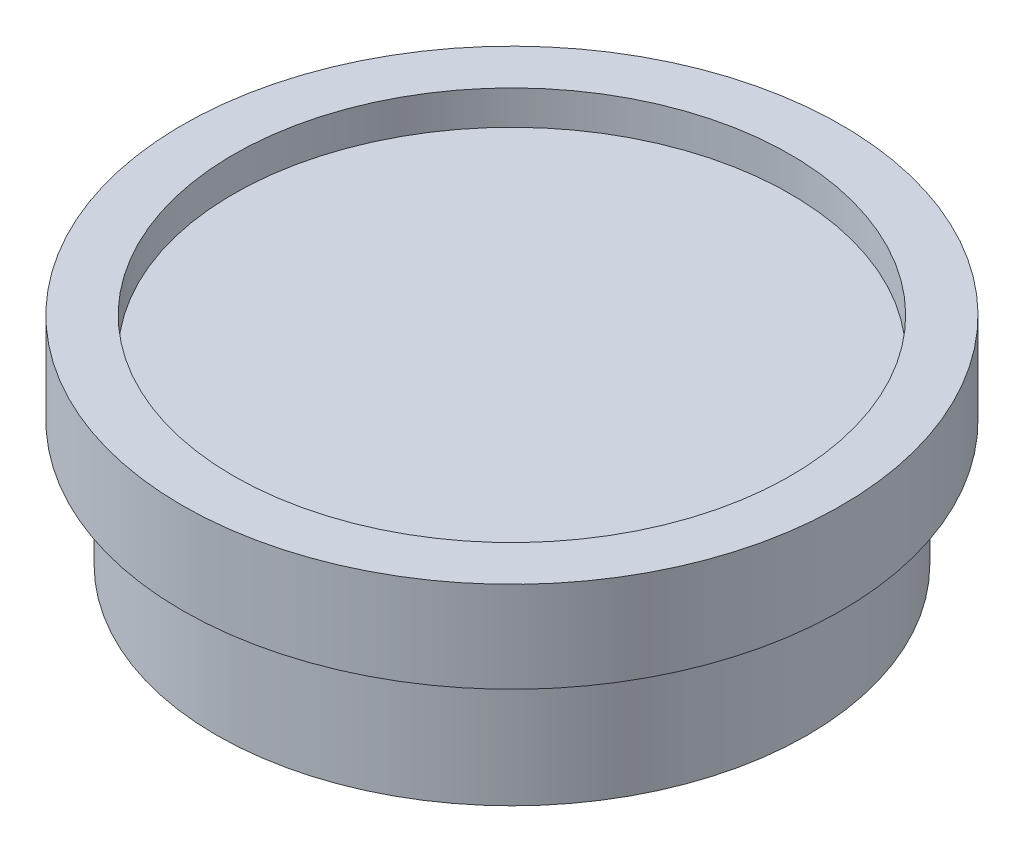
SolidWorks part; units mm, degrees
ref_plane "Front Plane" through (0, 0, 0) normal (0, 0, 1) x (1, 0, 0)
ref_plane "Top Plane" through (0, 0, 0) normal (0, 1, 0) x (1, 0, 0)
ref_plane "Right Plane" through (0, 0, 0) normal (1, 0, 0) x (0, 0, -1)
sketch "Sketch1" plane through (0, 0, 0) normal (0, 1, 0) x (1, 0, 0)
  circle A0 centre (0, 0) radius 29
  dimension "D1" = 58
extrude "Boss-Extrude1" add sketch "Sketch1" against normal blind 8
sketch "Sketch2" plane through (0, -8, 0) normal (0, -1, 0) x (1, 0, 0)
  circle A0 centre (0, 0) radius 26
  dimension "D1" = 52
extrude "Boss-Extrude2" add sketch "Sketch2" along normal blind 11
sketch "Sketch3" plane through (0, 0, 0) normal (0, 1, 0) x (1, 0, 0)
  circle A0 centre (0, 0) radius 24.5
  dimension "D1" = 49
extrude "Cut-Extrude1" cut sketch "Sketch3" against normal blind 3
